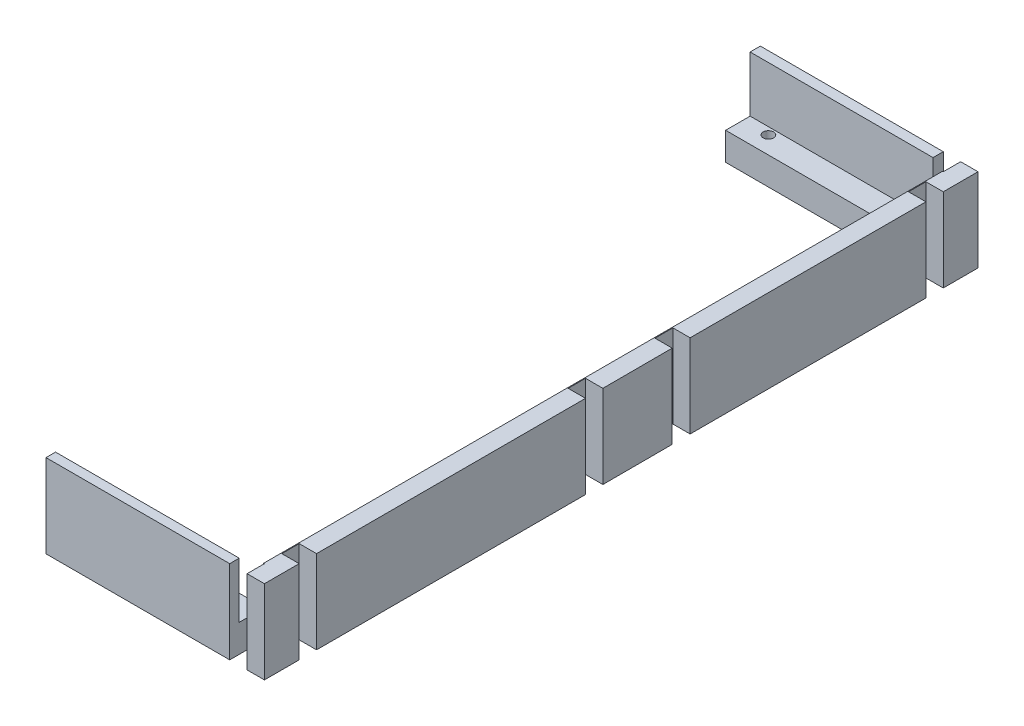
SolidWorks part; units mm, degrees
ref_plane "Front Plane" through (0, 0, 0) normal (0, 0, 1) x (1, 0, 0)
ref_plane "Top Plane" through (0, 0, 0) normal (0, 1, 0) x (1, 0, 0)
ref_plane "Right Plane" through (0, 0, 0) normal (1, 0, 0) x (0, 0, -1)
sketch "Sketch2" plane through (0, 6.35, 0) normal (0, 1, 0) x (1, 0, 0)
  line L0 (104.775, 124.4785) -> (-29.0195, 124.4785) construction
  line L1 (37.8777, 124.4785) -> (104.775, 124.4785)
  line L2 (37.8777, 124.4785) -> (37.8777, 111.7785)
  line L3 (37.8777, 111.7785) -> (104.775, 111.7785)
  line L5 (111.125, -123.7602) -> (117.475, -123.7602) construction
  line L11 (117.475, 124.4785) -> (117.475, 111.7785)
  line L14 (104.775, -123.7602) -> (37.5983, -123.7602)
  line L16 (117.475, -123.7602) -> (117.475, -136.4602)
  line L17 (111.125, 118.1285) -> (104.775, 118.1285) construction
  line L18 (111.125, 118.1285) -> (111.125, 124.4785) construction
  line L20 (104.775, 118.1285) -> (104.775, 124.4785) construction
  line L21 (117.475, 105.4285) -> (111.125, 105.4285) construction
  line L23 (117.475, 111.7785) -> (111.125, 111.7785) construction
  line L25 (117.4276, 12.7) -> (111.125, 12.7) construction
  line L27 (117.4276, 19.2555) -> (111.125, 19.2555) construction
  line L38 (111.125, -136.4602) -> (111.125, -130.1018) construction
  line L39 (111.125, -130.1018) -> (104.775, -130.1018) construction
  line L40 (104.775, -136.4602) -> (104.775, -130.1018) construction
  line L42 (104.775, -123.7602) -> (104.775, -111.031)
  line L43 (117.475, -19.05) -> (117.475, -117.4102)
  line L48 (111.125, -12.7) -> (117.475, -12.7) construction
  line L50 (111.125, -19.05) -> (117.475, -19.05) construction
  line L52 (37.5983, -123.7602) -> (37.5983, -136.4602)
  line L53 (117.475, -136.4602) -> (111.125, -136.4602)
  line L59 (104.775, 105.4285) -> (104.775, 111.7785)
  line L60 (117.475, 111.7785) -> (111.125, 111.7785)
  line L61 (111.125, 111.7785) -> (111.125, 105.4285)
  line L62 (117.475, 105.4285) -> (111.125, 105.4285)
  line L63 (104.775, 105.4285) -> (104.775, 99.0373)
  line L65 (111.125, 124.4785) -> (117.475, 124.4785)
  line L66 (104.775, 124.4785) -> (104.775, 118.1285)
  line L67 (104.775, 118.1285) -> (111.125, 118.1285)
  line L68 (111.125, 118.1285) -> (111.125, 124.4785)
  line L69 (117.4276, 19.2555) -> (111.125, 19.2555)
  line L71 (104.775, 25.572) -> (104.775, 19.2555)
  line L72 (104.775, 19.2555) -> (104.775, -24.9507)
  line L74 (117.4276, 12.7) -> (117.475, -12.7)
  line L76 (111.125, 19.2555) -> (111.125, 12.7)
  line L77 (111.125, 12.7) -> (117.4276, 12.7)
  line L79 (111.125, -19.05) -> (117.475, -19.05)
  line L80 (111.125, -12.7) -> (111.125, -19.05)
  line L81 (117.475, 105.4285) -> (117.4276, 19.2555)
  line L82 (117.475, -12.7) -> (111.125, -12.7)
  line L84 (111.125, -117.4102) -> (111.125, -123.7602)
  line L85 (117.475, -117.4102) -> (111.125, -117.4102)
  line L86 (111.125, -123.7602) -> (117.475, -123.7602)
  line L87 (104.775, -136.4602) -> (37.5983, -136.4602)
  line L88 (104.775, -136.4602) -> (104.775, -130.1018)
  line L89 (104.775, -130.1018) -> (111.125, -130.1018)
  line L90 (111.125, -130.1018) -> (111.125, -136.4602)
  line L91 (104.775, -24.9507) -> (104.775, -111.031)
  line L92 (104.775, 25.572) -> (104.775, 99.0373)
  circle A0 centre (47.1805, 118.1285) radius 1.905 construction
  circle A1 centre (45.6235, -130.1018) radius 1.905 construction
  circle A2 centre (45.6235, -130.1018) radius 1.905
  circle A3 centre (47.1805, 118.1285) radius 1.905
extrude "Boss-Extrude5" add sketch "Sketch2" along normal blind 30.48
sketch "Sketch3" plane through (0, 36.83, 0) normal (0, 1, 0) x (1, 0, 0)
  line L1 (33.7077, 120.7375) -> (110.8467, 120.7375)
  line L2 (33.7077, 120.7375) -> (33.7077, -132.9697)
  line L3 (33.7077, -132.9697) -> (110.8467, -132.9697)
  line L4 (110.8467, 120.7375) -> (110.8467, -132.9697)
extrude "Cut-Extrude1" cut sketch "Sketch3" against normal offset from surface (20.32 mm away) 20.32 up to face at (45.6235, 36.83, 132.0068)
